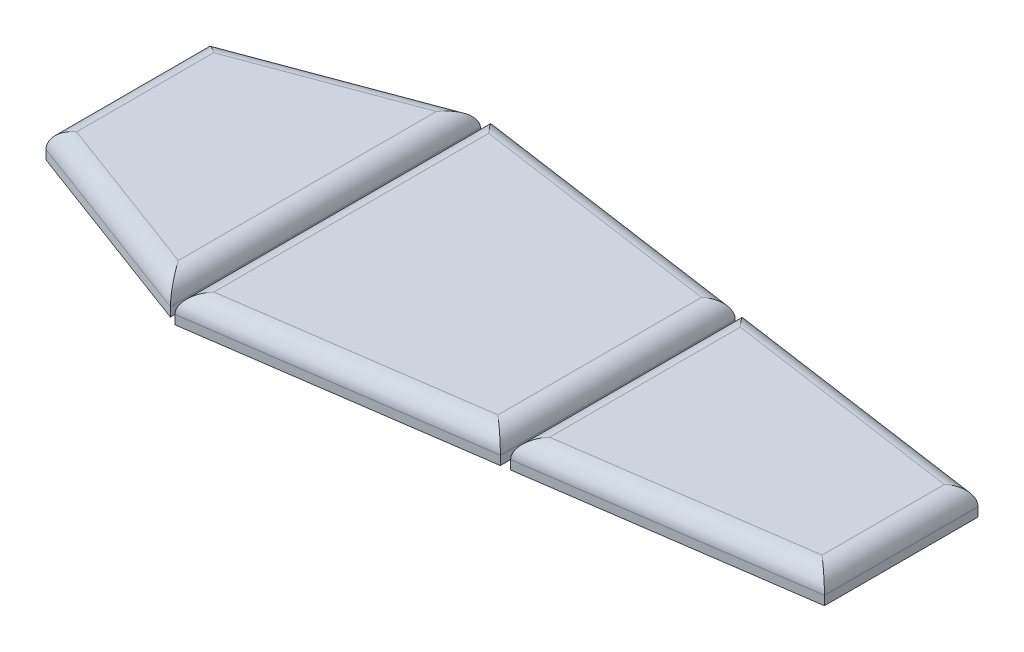
SolidWorks part; units mm, degrees
ref_plane "Front Plane" through (0, 0, 0) normal (0, 0, 1) x (1, 0, 0)
ref_plane "Top Plane" through (0, 0, 0) normal (0, 1, 0) x (1, 0, 0)
ref_plane "Right Plane" through (0, 0, 0) normal (1, 0, 0) x (0, 0, -1)
sketch "Sketch2" plane through (0, 14.2875, 0) normal (0, 1, 0) x (1, 0, 0)
  line L0 (-1148.1283, 239.4546) -> (-589.3283, 447.7752)
  line L1 (-589.3283, 447.7752) -> (-589.3283, -425.648)
  line L2 (-589.3283, -425.648) -> (-1148.1283, -217.3134)
  line L3 (-1148.1283, -217.3134) -> (-1148.1283, 239.4546)
  line L4 (-1198.9283, 268.1104) -> (-1198.9283, -252.5896) construction
  line L5 (-563.9283, 504.8384) -> (-1198.9283, 268.1104) construction
  line L6 (-1198.9283, -252.5896) -> (-563.9283, -489.3335) construction
  dimension "D1" = 44.5958
  dimension "D2" = 50.8
  dimension "D3" = 50.8
  dimension "D4" = 25.4
extrude "Boss-Extrude3" add sketch "Sketch2" along normal blind 76.2
sketch "Sketch3" plane through (0, 14.2875, 0) normal (0, 1, 0) x (1, 0, 0)
  line L0 (-563.9283, 453.5188) -> (-563.9283, -438.0139)
  line L1 (-563.9283, -438.0139) -> (237.7667, -323.0554)
  line L2 (237.7667, -323.0554) -> (237.7667, 338.5681)
  line L3 (237.7667, 338.5681) -> (-563.9283, 453.5188)
  line L4 (1087.0717, 268.1104) -> (-563.9283, 504.8384) construction
  line L5 (-563.9283, -489.3335) -> (1087.0717, -252.5896) construction
  line L6 (-589.3283, -425.648) -> (-589.3283, 447.7752) construction
  line L7 (-589.3283, -425.648) -> (-589.3283, 447.7752) construction
  dimension "D1" = 25.4
  dimension "D2" = 50.8
  dimension "D3" = 50.8
extrude "Boss-Extrude4" add sketch "Sketch3" along normal blind 76.2
sketch "Sketch4" plane through (0, 14.2875, 0) normal (0, 1, 0) x (1, 0, 0)
  line L0 (263.1667, 334.9261) -> (263.1667, -319.4132)
  line L1 (263.1667, -319.4132) -> (1036.2717, -208.5544)
  line L2 (1036.2717, -208.5544) -> (1036.2717, 224.0748)
  line L3 (1036.2717, 224.0748) -> (263.1667, 334.9261)
  line L4 (1087.0717, 268.1104) -> (-563.9283, 504.8384) construction
  line L5 (-563.9283, -489.3335) -> (1087.0717, -252.5896) construction
  line L6 (1087.0717, -252.5896) -> (1087.0717, 268.1104) construction
  line L7 (237.7667, -323.0554) -> (237.7667, 338.5681) construction
  dimension "D1" = 25.4
  dimension "D2" = 50.8
  dimension "D3" = 50.8
  dimension "D4" = 50.8
extrude "Boss-Extrude5" add sketch "Sketch4" along normal blind 76.2
fillet "Fillet2" radius 50.8 4 edges at (-589.3283, 90.4875, -11.0636) (-868.7283, 90.4875, -343.6149) (-868.7283, 90.4875, 321.4807) (-1148.1283, 90.4875, -11.0706)
fillet "Fillet3" radius 50.8 4 edges at (-163.0808, 90.4875, -396.0435) (237.7667, 90.4875, -7.7563) (-163.0808, 90.4875, 380.5347) (-563.9283, 90.4875, -7.7525)
fillet "Fillet4" radius 50.8 4 edges at (649.7192, 90.4875, 263.9838) (1036.2717, 90.4875, -7.7602) (649.7192, 90.4875, -279.5005) (263.1667, 90.4875, -7.7565)
